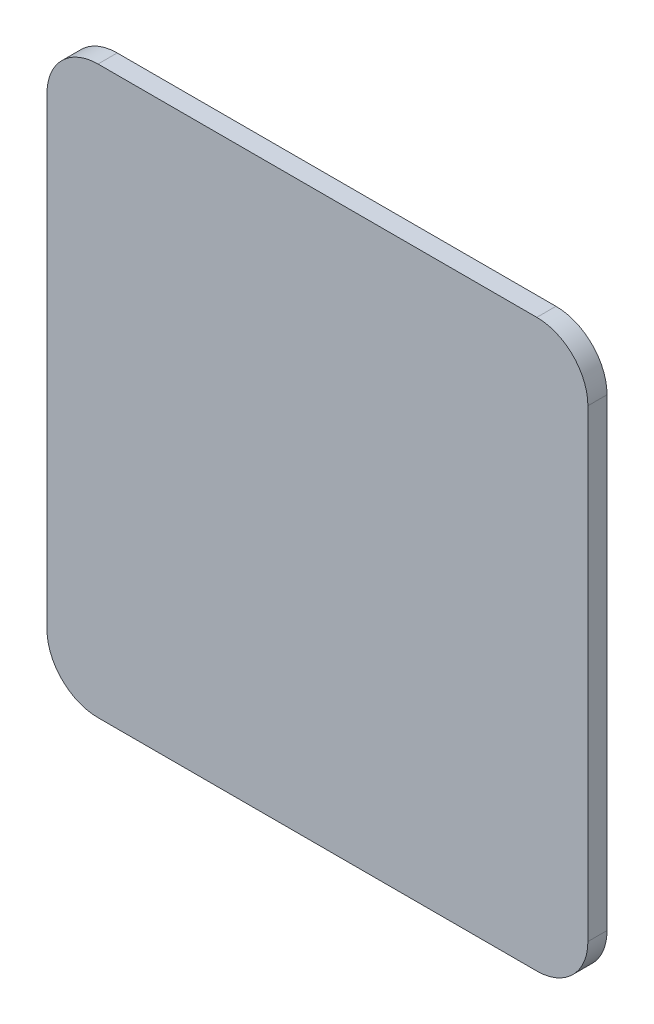
SolidWorks part; units mm, degrees
material "PC High Viscosity"
ref_plane "Front Plane" through (0, 0, 0) normal (0, 0, 1) x (1, 0, 0)
ref_plane "Top Plane" through (0, 0, 0) normal (0, 1, 0) x (1, 0, 0)
ref_plane "Right Plane" through (0, 0, 0) normal (1, 0, 0) x (0, 0, -1)
sketch "Sketch1" plane through (0, 0, 0) normal (0, 0, 1) x (1, 0, 0)
  line L0 (-26, 10) -> (-163.5, 10)
  line L1 (-179.5, 26) -> (-179.5, 171.4)
  line L2 (-179.5, 171.4) -> (-179.5, 26) construction
  line L3 (-163.5, 187.4) -> (-26, 187.4)
  line L4 (-10, 171.4) -> (-10, 26)
  arc A0 (-163.5, 10) -> (-179.5, 26) centre (-163.5, 26) cw
  arc A1 (-163.5, 187.4) -> (-179.5, 171.4) centre (-163.5, 171.4) ccw construction
  arc A2 (-179.5, 171.4) -> (-163.5, 187.4) centre (-163.5, 171.4) cw
  arc A3 (-26, 187.4) -> (-10, 171.4) centre (-26, 171.4) cw
  arc A4 (-10, 26) -> (-26, 10) centre (-26, 26) cw
extrude "Boss-Extrude1" add sketch "Sketch1" along normal blind 6
